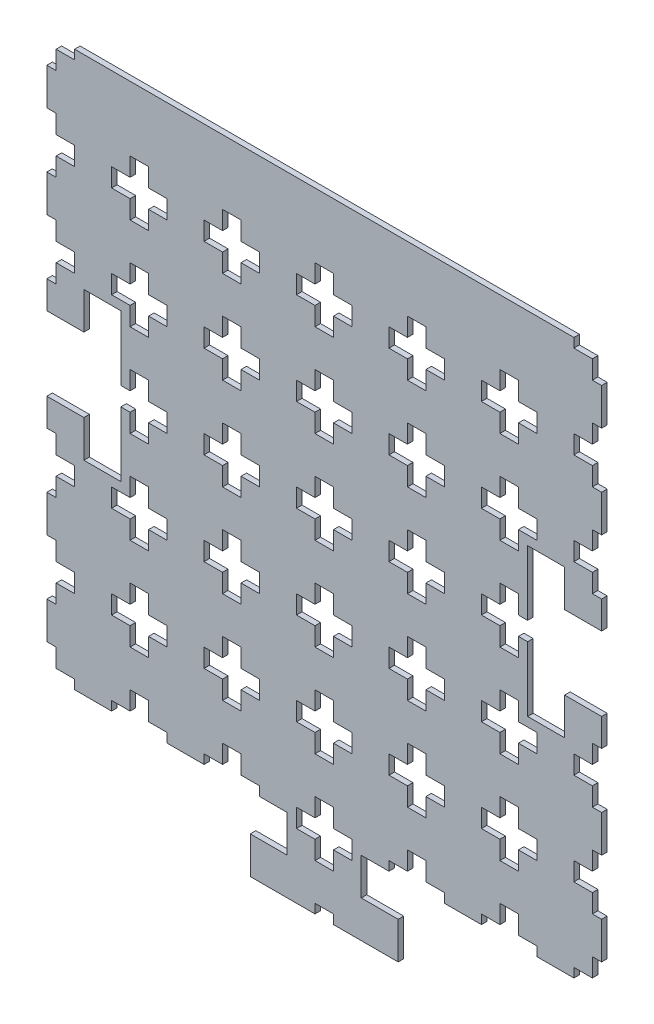
SolidWorks part; units mm, degrees
ref_plane "Plan de face" through (0, 0, 0) normal (0, 0, 1) x (1, 0, 0)
ref_plane "Plan de dessus" through (0, 0, 0) normal (0, 1, 0) x (1, 0, 0)
ref_plane "Plan de droite" through (0, 0, 0) normal (1, 0, 0) x (0, 0, -1)
sketch "Esquisse1" plane through (0, 0, 0) normal (0, 0, 1) x (1, 0, 0)
  line L1 (-218.6403, 173.0618) -> (81.3597, 173.0618)
  line L2 (-218.6403, 173.0618) -> (-218.6403, -126.9382)
  line L3 (-218.6403, -126.9382) -> (81.3597, -126.9382)
  line L4 (81.3597, 173.0618) -> (81.3597, -126.9382)
  dimension "D1" = 300
  dimension "D2" = 300
extrude "Boss.-Extru.1" add sketch "Esquisse1" along normal blind 3
sketch "Esquisse2" plane through (0, 0, 0) normal (0, 0, -1) x (-1, 0, 0)
  line L0 (-81.3597, 138.0618) -> (-76.3597, 138.0618)
  line L2 (-81.3597, -126.9382) -> (-81.3597, 173.0618) construction
  line L3 (-76.3597, 138.0618) -> (-76.3597, 128.0618)
  line L4 (-76.3597, 128.0618) -> (-66.3597, 128.0618)
  line L5 (-66.3597, 128.0618) -> (-66.3597, 118.0618)
  line L6 (-66.3597, 118.0618) -> (-76.3597, 118.0618)
  line L7 (-76.3597, 118.0618) -> (-76.3597, 108.0618)
  line L8 (13.6403, 128.0618) -> (13.6403, 138.0618)
  line L9 (-76.3597, 108.0618) -> (-81.3597, 108.0618)
  line L10 (-81.3597, 88.0618) -> (-76.3597, 88.0618)
  line L11 (-76.3597, 88.0618) -> (-76.3597, 78.0618)
  line L12 (-76.3597, 78.0618) -> (-66.3597, 78.0618)
  line L13 (-66.3597, 78.0618) -> (-66.3597, 68.0618)
  line L14 (-66.3597, 68.0618) -> (-76.3597, 68.0618)
  line L15 (-76.3597, 68.0618) -> (-76.3597, 58.0618)
  line L16 (-76.3597, 58.0618) -> (-81.3597, 58.0618)
  line L17 (-81.3597, 38.0618) -> (-76.3597, 38.0618)
  line L18 (-76.3597, 38.0618) -> (-76.3597, 28.0618)
  line L19 (-76.3597, 28.0618) -> (-66.3597, 28.0618)
  line L20 (-66.3597, 28.0618) -> (-66.3597, 18.0618)
  line L21 (-66.3597, 18.0618) -> (-76.3597, 18.0618)
  line L22 (-76.3597, 18.0618) -> (-76.3597, 8.0618)
  line L23 (-76.3597, 8.0618) -> (-81.3597, 8.0618)
  line L24 (-81.3597, -11.9382) -> (-76.3597, -11.9382)
  line L25 (-76.3597, -11.9382) -> (-76.3597, -21.9382)
  line L26 (-76.3597, -21.9382) -> (-66.3597, -21.9382)
  line L27 (-66.3597, -21.9382) -> (-66.3597, -31.9382)
  line L28 (-66.3597, -31.9382) -> (-76.3597, -31.9382)
  line L29 (-76.3597, -31.9382) -> (-76.3597, -41.9382)
  line L30 (-76.3597, -41.9382) -> (-81.3597, -41.9382)
  line L31 (-81.3597, -61.9382) -> (-76.3597, -61.9382)
  line L32 (-76.3597, -61.9382) -> (-76.3597, -71.9382)
  line L33 (-76.3597, -71.9382) -> (-66.3597, -71.9382)
  line L34 (-66.3597, -71.9382) -> (-66.3597, -81.9382)
  line L35 (-66.3597, -81.9382) -> (-76.3597, -81.9382)
  line L36 (-76.3597, -81.9382) -> (-76.3597, -91.9382)
  line L37 (-76.3597, -91.9382) -> (-81.3597, -91.9382)
  line L38 (-81.3597, -111.9382) -> (-76.3597, -111.9382)
  line L39 (-76.3597, -111.9382) -> (-76.3597, -121.9382)
  line L40 (-76.3597, -121.9382) -> (-66.3597, -121.9382)
  line L41 (-66.3597, -121.9382) -> (-66.3597, -126.9382)
  line L42 (218.6403, -126.9382) -> (-81.3597, -126.9382) construction
  line L43 (-81.3597, 173.0618) -> (218.6403, 173.0618) construction
  line L45 (-66.3597, -131.9382) -> (-76.3597, -131.9382) [skipped]
  line L46 (-76.3597, -131.9382) -> (-76.3597, -141.9382) [skipped]
  line L47 (-76.3597, -141.9382) -> (-81.3597, -141.9382) [skipped]
  line L48 (-66.3597, -121.9382) -> (-66.3597, -131.9382) [skipped]
  line L61 (-36.3597, 128.0618) -> (-36.3597, 138.0618)
  line L62 (-36.3597, 138.0618) -> (-26.3597, 138.0618)
  line L63 (-26.3597, 138.0618) -> (-26.3597, 128.0618)
  line L64 (-26.3597, 128.0618) -> (-16.3597, 128.0618)
  line L65 (-16.3597, 128.0618) -> (-16.3597, 118.0618)
  line L66 (13.6403, 138.0618) -> (23.6403, 138.0618)
  line L67 (3.6403, 128.0618) -> (13.6403, 128.0618)
  line L68 (3.6403, 118.0618) -> (3.6403, 128.0618)
  line L69 (13.6403, 118.0618) -> (3.6403, 118.0618)
  line L70 (13.6403, 108.0618) -> (13.6403, 118.0618)
  line L71 (23.6403, 108.0618) -> (13.6403, 108.0618)
  line L72 (23.6403, 118.0618) -> (23.6403, 108.0618)
  line L73 (33.6403, 118.0618) -> (23.6403, 118.0618)
  line L74 (33.6403, 128.0618) -> (33.6403, 118.0618)
  line L75 (23.6403, 128.0618) -> (33.6403, 128.0618)
  line L76 (23.6403, 138.0618) -> (23.6403, 128.0618)
  line L77 (63.6403, 128.0618) -> (63.6403, 138.0618)
  line L78 (63.6403, 138.0618) -> (73.6403, 138.0618)
  line L79 (53.6403, 128.0618) -> (63.6403, 128.0618)
  line L80 (53.6403, 118.0618) -> (53.6403, 128.0618)
  line L81 (63.6403, 118.0618) -> (53.6403, 118.0618)
  line L82 (63.6403, 108.0618) -> (63.6403, 118.0618)
  line L83 (73.6403, 108.0618) -> (63.6403, 108.0618)
  line L84 (73.6403, 118.0618) -> (73.6403, 108.0618)
  line L85 (83.6403, 118.0618) -> (73.6403, 118.0618)
  line L86 (83.6403, 128.0618) -> (83.6403, 118.0618)
  line L87 (73.6403, 128.0618) -> (83.6403, 128.0618)
  line L88 (73.6403, 138.0618) -> (73.6403, 128.0618)
  line L89 (113.6403, 128.0618) -> (113.6403, 138.0618)
  line L90 (113.6403, 138.0618) -> (123.6403, 138.0618)
  line L91 (103.6403, 128.0618) -> (113.6403, 128.0618)
  line L92 (103.6403, 118.0618) -> (103.6403, 128.0618)
  line L93 (113.6403, 118.0618) -> (103.6403, 118.0618)
  line L94 (113.6403, 108.0618) -> (113.6403, 118.0618)
  line L95 (123.6403, 108.0618) -> (113.6403, 108.0618)
  line L96 (123.6403, 118.0618) -> (123.6403, 108.0618)
  line L97 (133.6403, 118.0618) -> (123.6403, 118.0618)
  line L98 (133.6403, 128.0618) -> (133.6403, 118.0618)
  line L99 (123.6403, 128.0618) -> (133.6403, 128.0618)
  line L100 (123.6403, 138.0618) -> (123.6403, 128.0618)
  line L101 (163.6403, 128.0618) -> (163.6403, 138.0618)
  line L102 (163.6403, 138.0618) -> (173.6403, 138.0618)
  line L103 (153.6403, 128.0618) -> (163.6403, 128.0618)
  line L104 (153.6403, 118.0618) -> (153.6403, 128.0618)
  line L105 (163.6403, 118.0618) -> (153.6403, 118.0618)
  line L106 (163.6403, 108.0618) -> (163.6403, 118.0618)
  line L107 (173.6403, 108.0618) -> (163.6403, 108.0618)
  line L108 (173.6403, 118.0618) -> (173.6403, 108.0618)
  line L109 (183.6403, 118.0618) -> (173.6403, 118.0618)
  line L110 (183.6403, 128.0618) -> (183.6403, 118.0618)
  line L111 (173.6403, 128.0618) -> (183.6403, 128.0618)
  line L112 (173.6403, 138.0618) -> (173.6403, 128.0618)
  line L113 (213.6403, 128.0618) -> (213.6403, 138.0618)
  line L114 (213.6403, 138.0618) -> (223.6403, 138.0618)
  line L115 (203.6403, 128.0618) -> (213.6403, 128.0618)
  line L116 (203.6403, 118.0618) -> (203.6403, 128.0618)
  line L117 (213.6403, 118.0618) -> (203.6403, 118.0618)
  line L118 (213.6403, 108.0618) -> (213.6403, 118.0618)
  line L119 (223.6403, 108.0618) -> (213.6403, 108.0618)
  line L120 (223.6403, 118.0618) -> (223.6403, 108.0618)
  line L121 (233.6403, 118.0618) -> (223.6403, 118.0618)
  line L122 (233.6403, 128.0618) -> (233.6403, 118.0618)
  line L123 (223.6403, 128.0618) -> (233.6403, 128.0618)
  line L124 (223.6403, 138.0618) -> (223.6403, 128.0618)
  line L180 (218.6403, 173.0618) -> (218.6403, -126.9382) construction
  line L186 (13.6403, 78.0618) -> (13.6403, 88.0618)
  line L187 (13.6403, 88.0618) -> (23.6403, 88.0618)
  line L188 (3.6403, 78.0618) -> (13.6403, 78.0618)
  line L189 (3.6403, 68.0618) -> (3.6403, 78.0618)
  line L190 (13.6403, 68.0618) -> (3.6403, 68.0618)
  line L191 (13.6403, 58.0618) -> (13.6403, 68.0618)
  line L192 (23.6403, 58.0618) -> (13.6403, 58.0618)
  line L193 (23.6403, 68.0618) -> (23.6403, 58.0618)
  line L194 (33.6403, 68.0618) -> (23.6403, 68.0618)
  line L195 (33.6403, 78.0618) -> (33.6403, 68.0618)
  line L196 (23.6403, 78.0618) -> (33.6403, 78.0618)
  line L197 (23.6403, 88.0618) -> (23.6403, 78.0618)
  line L198 (63.6403, 78.0618) -> (63.6403, 88.0618)
  line L199 (63.6403, 88.0618) -> (73.6403, 88.0618)
  line L200 (53.6403, 78.0618) -> (63.6403, 78.0618)
  line L201 (53.6403, 68.0618) -> (53.6403, 78.0618)
  line L202 (63.6403, 68.0618) -> (53.6403, 68.0618)
  line L203 (63.6403, 58.0618) -> (63.6403, 68.0618)
  line L204 (73.6403, 58.0618) -> (63.6403, 58.0618)
  line L205 (73.6403, 68.0618) -> (73.6403, 58.0618)
  line L206 (83.6403, 68.0618) -> (73.6403, 68.0618)
  line L207 (83.6403, 78.0618) -> (83.6403, 68.0618)
  line L208 (73.6403, 78.0618) -> (83.6403, 78.0618)
  line L209 (73.6403, 88.0618) -> (73.6403, 78.0618)
  line L210 (113.6403, 78.0618) -> (113.6403, 88.0618)
  line L211 (113.6403, 88.0618) -> (123.6403, 88.0618)
  line L212 (103.6403, 78.0618) -> (113.6403, 78.0618)
  line L213 (103.6403, 68.0618) -> (103.6403, 78.0618)
  line L214 (113.6403, 68.0618) -> (103.6403, 68.0618)
  line L215 (113.6403, 58.0618) -> (113.6403, 68.0618)
  line L216 (123.6403, 58.0618) -> (113.6403, 58.0618)
  line L217 (123.6403, 68.0618) -> (123.6403, 58.0618)
  line L218 (133.6403, 68.0618) -> (123.6403, 68.0618)
  line L219 (133.6403, 78.0618) -> (133.6403, 68.0618)
  line L220 (123.6403, 78.0618) -> (133.6403, 78.0618)
  line L221 (123.6403, 88.0618) -> (123.6403, 78.0618)
  line L222 (163.6403, 78.0618) -> (163.6403, 88.0618)
  line L223 (163.6403, 88.0618) -> (173.6403, 88.0618)
  line L224 (153.6403, 78.0618) -> (163.6403, 78.0618)
  line L225 (153.6403, 68.0618) -> (153.6403, 78.0618)
  line L226 (163.6403, 68.0618) -> (153.6403, 68.0618)
  line L227 (163.6403, 58.0618) -> (163.6403, 68.0618)
  line L228 (173.6403, 58.0618) -> (163.6403, 58.0618)
  line L229 (173.6403, 68.0618) -> (173.6403, 58.0618)
  line L230 (183.6403, 68.0618) -> (173.6403, 68.0618)
  line L231 (183.6403, 78.0618) -> (183.6403, 68.0618)
  line L232 (173.6403, 78.0618) -> (183.6403, 78.0618)
  line L233 (173.6403, 88.0618) -> (173.6403, 78.0618)
  line L234 (213.6403, 78.0618) -> (213.6403, 88.0618)
  line L235 (213.6403, 88.0618) -> (223.6403, 88.0618)
  line L236 (203.6403, 78.0618) -> (213.6403, 78.0618)
  line L237 (203.6403, 68.0618) -> (203.6403, 78.0618)
  line L238 (213.6403, 68.0618) -> (203.6403, 68.0618)
  line L239 (213.6403, 58.0618) -> (213.6403, 68.0618)
  line L240 (223.6403, 58.0618) -> (213.6403, 58.0618)
  line L241 (223.6403, 68.0618) -> (223.6403, 58.0618)
  line L242 (233.6403, 68.0618) -> (223.6403, 68.0618)
  line L243 (233.6403, 78.0618) -> (233.6403, 68.0618)
  line L244 (223.6403, 78.0618) -> (233.6403, 78.0618)
  line L245 (223.6403, 88.0618) -> (223.6403, 78.0618)
  line L246 (13.6403, 28.0618) -> (13.6403, 38.0618)
  line L247 (13.6403, 38.0618) -> (23.6403, 38.0618)
  line L248 (3.6403, 28.0618) -> (13.6403, 28.0618)
  line L249 (3.6403, 18.0618) -> (3.6403, 28.0618)
  line L250 (13.6403, 18.0618) -> (3.6403, 18.0618)
  line L251 (13.6403, 8.0618) -> (13.6403, 18.0618)
  line L252 (23.6403, 8.0618) -> (13.6403, 8.0618)
  line L253 (23.6403, 18.0618) -> (23.6403, 8.0618)
  line L254 (33.6403, 18.0618) -> (23.6403, 18.0618)
  line L255 (33.6403, 28.0618) -> (33.6403, 18.0618)
  line L256 (23.6403, 28.0618) -> (33.6403, 28.0618)
  line L257 (23.6403, 38.0618) -> (23.6403, 28.0618)
  line L258 (63.6403, 28.0618) -> (63.6403, 38.0618)
  line L259 (63.6403, 38.0618) -> (73.6403, 38.0618)
  line L260 (53.6403, 28.0618) -> (63.6403, 28.0618)
  line L261 (53.6403, 18.0618) -> (53.6403, 28.0618)
  line L262 (63.6403, 18.0618) -> (53.6403, 18.0618)
  line L263 (63.6403, 8.0618) -> (63.6403, 18.0618)
  line L264 (73.6403, 8.0618) -> (63.6403, 8.0618)
  line L265 (73.6403, 18.0618) -> (73.6403, 8.0618)
  line L266 (83.6403, 18.0618) -> (73.6403, 18.0618)
  line L267 (83.6403, 28.0618) -> (83.6403, 18.0618)
  line L268 (73.6403, 28.0618) -> (83.6403, 28.0618)
  line L269 (73.6403, 38.0618) -> (73.6403, 28.0618)
  line L270 (113.6403, 28.0618) -> (113.6403, 38.0618)
  line L271 (113.6403, 38.0618) -> (123.6403, 38.0618)
  line L272 (103.6403, 28.0618) -> (113.6403, 28.0618)
  line L273 (103.6403, 18.0618) -> (103.6403, 28.0618)
  line L274 (113.6403, 18.0618) -> (103.6403, 18.0618)
  line L275 (113.6403, 8.0618) -> (113.6403, 18.0618)
  line L276 (123.6403, 8.0618) -> (113.6403, 8.0618)
  line L277 (123.6403, 18.0618) -> (123.6403, 8.0618)
  line L278 (133.6403, 18.0618) -> (123.6403, 18.0618)
  line L279 (133.6403, 28.0618) -> (133.6403, 18.0618)
  line L280 (123.6403, 28.0618) -> (133.6403, 28.0618)
  line L281 (123.6403, 38.0618) -> (123.6403, 28.0618)
  line L282 (163.6403, 28.0618) -> (163.6403, 38.0618)
  line L283 (163.6403, 38.0618) -> (173.6403, 38.0618)
  line L284 (153.6403, 28.0618) -> (163.6403, 28.0618)
  line L285 (153.6403, 18.0618) -> (153.6403, 28.0618)
  line L286 (163.6403, 18.0618) -> (153.6403, 18.0618)
  line L287 (163.6403, 8.0618) -> (163.6403, 18.0618)
  line L288 (173.6403, 8.0618) -> (163.6403, 8.0618)
  line L289 (173.6403, 18.0618) -> (173.6403, 8.0618)
  line L290 (183.6403, 18.0618) -> (173.6403, 18.0618)
  line L291 (183.6403, 28.0618) -> (183.6403, 18.0618)
  line L292 (173.6403, 28.0618) -> (183.6403, 28.0618)
  line L293 (173.6403, 38.0618) -> (173.6403, 28.0618)
  line L294 (213.6403, 28.0618) -> (213.6403, 38.0618)
  line L295 (213.6403, 38.0618) -> (223.6403, 38.0618)
  line L296 (203.6403, 28.0618) -> (213.6403, 28.0618)
  line L297 (203.6403, 18.0618) -> (203.6403, 28.0618)
  line L298 (-66.3597, 173.0618) -> (-66.3597, 168.0618)
  line L299 (-66.3597, 168.0618) -> (-76.3597, 168.0618)
  line L300 (-76.3597, 168.0618) -> (-76.3597, 158.0618)
  line L301 (-76.3597, 158.0618) -> (-81.3597, 158.0618)
  line L302 (218.6403, 158.0618) -> (213.6403, 158.0618)
  line L303 (213.6403, 18.0618) -> (203.6403, 18.0618)
  line L304 (213.6403, 8.0618) -> (213.6403, 18.0618)
  line L305 (223.6403, 8.0618) -> (213.6403, 8.0618)
  line L306 (223.6403, 18.0618) -> (223.6403, 8.0618)
  line L307 (233.6403, 18.0618) -> (223.6403, 18.0618)
  line L308 (233.6403, 28.0618) -> (233.6403, 18.0618)
  line L309 (223.6403, 28.0618) -> (233.6403, 28.0618)
  line L310 (223.6403, 38.0618) -> (223.6403, 28.0618)
  line L311 (13.6403, -21.9382) -> (13.6403, -11.9382)
  line L312 (13.6403, -11.9382) -> (23.6403, -11.9382)
  line L313 (3.6403, -21.9382) -> (13.6403, -21.9382)
  line L314 (3.6403, -31.9382) -> (3.6403, -21.9382)
  line L315 (13.6403, -31.9382) -> (3.6403, -31.9382)
  line L316 (13.6403, -41.9382) -> (13.6403, -31.9382)
  line L317 (23.6403, -41.9382) -> (13.6403, -41.9382)
  line L318 (23.6403, -31.9382) -> (23.6403, -41.9382)
  line L319 (33.6403, -31.9382) -> (23.6403, -31.9382)
  line L320 (33.6403, -21.9382) -> (33.6403, -31.9382)
  line L321 (23.6403, -21.9382) -> (33.6403, -21.9382)
  line L322 (23.6403, -11.9382) -> (23.6403, -21.9382)
  line L323 (63.6403, -21.9382) -> (63.6403, -11.9382)
  line L324 (63.6403, -11.9382) -> (73.6403, -11.9382)
  line L325 (53.6403, -21.9382) -> (63.6403, -21.9382)
  line L326 (53.6403, -31.9382) -> (53.6403, -21.9382)
  line L327 (63.6403, -31.9382) -> (53.6403, -31.9382)
  line L328 (63.6403, -41.9382) -> (63.6403, -31.9382)
  line L329 (73.6403, -41.9382) -> (63.6403, -41.9382)
  line L330 (73.6403, -31.9382) -> (73.6403, -41.9382)
  line L331 (83.6403, -31.9382) -> (73.6403, -31.9382)
  line L332 (83.6403, -21.9382) -> (83.6403, -31.9382)
  line L333 (73.6403, -21.9382) -> (83.6403, -21.9382)
  line L334 (73.6403, -11.9382) -> (73.6403, -21.9382)
  line L335 (113.6403, -21.9382) -> (113.6403, -11.9382)
  line L336 (113.6403, -11.9382) -> (123.6403, -11.9382)
  line L337 (103.6403, -21.9382) -> (113.6403, -21.9382)
  line L338 (103.6403, -31.9382) -> (103.6403, -21.9382)
  line L339 (113.6403, -31.9382) -> (103.6403, -31.9382)
  line L340 (113.6403, -41.9382) -> (113.6403, -31.9382)
  line L341 (123.6403, -41.9382) -> (113.6403, -41.9382)
  line L342 (123.6403, -31.9382) -> (123.6403, -41.9382)
  line L343 (133.6403, -31.9382) -> (123.6403, -31.9382)
  line L344 (133.6403, -21.9382) -> (133.6403, -31.9382)
  line L345 (123.6403, -21.9382) -> (133.6403, -21.9382)
  line L346 (123.6403, -11.9382) -> (123.6403, -21.9382)
  line L347 (163.6403, -21.9382) -> (163.6403, -11.9382)
  line L348 (163.6403, -11.9382) -> (173.6403, -11.9382)
  line L349 (153.6403, -21.9382) -> (163.6403, -21.9382)
  line L350 (153.6403, -31.9382) -> (153.6403, -21.9382)
  line L351 (163.6403, -31.9382) -> (153.6403, -31.9382)
  line L352 (163.6403, -41.9382) -> (163.6403, -31.9382)
  line L353 (173.6403, -41.9382) -> (163.6403, -41.9382)
  line L354 (173.6403, -31.9382) -> (173.6403, -41.9382)
  line L355 (183.6403, -31.9382) -> (173.6403, -31.9382)
  line L356 (213.6403, 158.0618) -> (213.6403, 168.0618)
  line L357 (213.6403, 168.0618) -> (203.6403, 168.0618)
  line L358 (203.6403, 168.0618) -> (203.6403, 173.0618)
  line L363 (183.6403, -21.9382) -> (183.6403, -31.9382)
  line L364 (173.6403, -21.9382) -> (183.6403, -21.9382)
  line L365 (-16.3597, 118.0618) -> (-26.3597, 118.0618)
  line L366 (173.6403, -11.9382) -> (173.6403, -21.9382)
  line L367 (213.6403, -21.9382) -> (213.6403, -11.9382)
  line L368 (213.6403, -11.9382) -> (223.6403, -11.9382)
  line L369 (203.6403, -21.9382) -> (213.6403, -21.9382)
  line L370 (203.6403, -31.9382) -> (203.6403, -21.9382)
  line L371 (-26.3597, 118.0618) -> (-26.3597, 108.0618)
  line L372 (-26.3597, 108.0618) -> (-36.3597, 108.0618)
  line L373 (-36.3597, 108.0618) -> (-36.3597, 118.0618)
  line L374 (-36.3597, 118.0618) -> (-46.3597, 118.0618)
  line L375 (-46.3597, 118.0618) -> (-46.3597, 128.0618)
  line L376 (-46.3597, 128.0618) -> (-36.3597, 128.0618)
  line L377 (213.6403, -31.9382) -> (203.6403, -31.9382)
  line L378 (213.6403, -41.9382) -> (213.6403, -31.9382)
  line L379 (223.6403, -41.9382) -> (213.6403, -41.9382)
  line L380 (223.6403, -31.9382) -> (223.6403, -41.9382)
  line L381 (233.6403, -31.9382) -> (223.6403, -31.9382)
  line L382 (233.6403, -21.9382) -> (233.6403, -31.9382)
  line L383 (223.6403, -21.9382) -> (233.6403, -21.9382)
  line L384 (223.6403, -11.9382) -> (223.6403, -21.9382)
  line L385 (13.6403, -71.9382) -> (13.6403, -61.9382)
  line L386 (13.6403, -61.9382) -> (23.6403, -61.9382)
  line L387 (3.6403, -71.9382) -> (13.6403, -71.9382)
  line L388 (3.6403, -81.9382) -> (3.6403, -71.9382)
  line L389 (13.6403, -81.9382) -> (3.6403, -81.9382)
  line L390 (13.6403, -91.9382) -> (13.6403, -81.9382)
  line L391 (23.6403, -91.9382) -> (13.6403, -91.9382)
  line L392 (23.6403, -81.9382) -> (23.6403, -91.9382)
  line L393 (33.6403, -81.9382) -> (23.6403, -81.9382)
  line L394 (33.6403, -71.9382) -> (33.6403, -81.9382)
  line L395 (23.6403, -71.9382) -> (33.6403, -71.9382)
  line L396 (23.6403, -61.9382) -> (23.6403, -71.9382)
  line L397 (63.6403, -71.9382) -> (63.6403, -61.9382)
  line L398 (63.6403, -61.9382) -> (73.6403, -61.9382)
  line L399 (53.6403, -71.9382) -> (63.6403, -71.9382)
  line L400 (53.6403, -81.9382) -> (53.6403, -71.9382)
  line L401 (63.6403, -81.9382) -> (53.6403, -81.9382)
  line L402 (63.6403, -91.9382) -> (63.6403, -81.9382)
  line L403 (73.6403, -91.9382) -> (63.6403, -91.9382)
  line L404 (73.6403, -81.9382) -> (73.6403, -91.9382)
  line L405 (83.6403, -81.9382) -> (73.6403, -81.9382)
  line L406 (83.6403, -71.9382) -> (83.6403, -81.9382)
  line L407 (73.6403, -71.9382) -> (83.6403, -71.9382)
  line L408 (73.6403, -61.9382) -> (73.6403, -71.9382)
  line L409 (113.6403, -71.9382) -> (113.6403, -61.9382)
  line L410 (113.6403, -61.9382) -> (123.6403, -61.9382)
  line L411 (103.6403, -71.9382) -> (113.6403, -71.9382)
  line L412 (103.6403, -81.9382) -> (103.6403, -71.9382)
  line L413 (113.6403, -81.9382) -> (103.6403, -81.9382)
  line L414 (113.6403, -91.9382) -> (113.6403, -81.9382)
  line L415 (123.6403, -91.9382) -> (113.6403, -91.9382)
  line L416 (123.6403, -81.9382) -> (123.6403, -91.9382)
  line L417 (133.6403, -81.9382) -> (123.6403, -81.9382)
  line L418 (133.6403, -71.9382) -> (133.6403, -81.9382)
  line L419 (123.6403, -71.9382) -> (133.6403, -71.9382)
  line L420 (123.6403, -61.9382) -> (123.6403, -71.9382)
  line L421 (163.6403, -71.9382) -> (163.6403, -61.9382)
  line L422 (163.6403, -61.9382) -> (173.6403, -61.9382)
  line L423 (153.6403, -71.9382) -> (163.6403, -71.9382)
  line L424 (153.6403, -81.9382) -> (153.6403, -71.9382)
  line L425 (163.6403, -81.9382) -> (153.6403, -81.9382)
  line L426 (163.6403, -91.9382) -> (163.6403, -81.9382)
  line L427 (173.6403, -91.9382) -> (163.6403, -91.9382)
  line L428 (173.6403, -81.9382) -> (173.6403, -91.9382)
  line L429 (183.6403, -81.9382) -> (173.6403, -81.9382)
  line L430 (183.6403, -71.9382) -> (183.6403, -81.9382)
  line L431 (173.6403, -71.9382) -> (183.6403, -71.9382)
  line L432 (173.6403, -61.9382) -> (173.6403, -71.9382)
  line L433 (213.6403, -71.9382) -> (213.6403, -61.9382)
  line L434 (213.6403, -61.9382) -> (223.6403, -61.9382)
  line L435 (203.6403, -71.9382) -> (213.6403, -71.9382)
  line L436 (203.6403, -81.9382) -> (203.6403, -71.9382)
  line L437 (213.6403, -81.9382) -> (203.6403, -81.9382)
  line L438 (213.6403, -91.9382) -> (213.6403, -81.9382)
  line L439 (223.6403, -91.9382) -> (213.6403, -91.9382)
  line L440 (223.6403, -81.9382) -> (223.6403, -91.9382)
  line L441 (233.6403, -81.9382) -> (223.6403, -81.9382)
  line L442 (233.6403, -71.9382) -> (233.6403, -81.9382)
  line L443 (223.6403, -71.9382) -> (233.6403, -71.9382)
  line L444 (223.6403, -61.9382) -> (223.6403, -71.9382)
  line L445 (13.6403, -121.9382) -> (13.6403, -111.9382)
  line L446 (13.6403, -111.9382) -> (23.6403, -111.9382)
  line L447 (3.6403, -121.9382) -> (13.6403, -121.9382)
  line L448 (3.6403, -131.9382) -> (3.6403, -121.9382)
  line L449 (13.6403, -131.9382) -> (3.6403, -131.9382)
  line L450 (13.6403, -141.9382) -> (13.6403, -131.9382)
  line L451 (23.6403, -141.9382) -> (13.6403, -141.9382)
  line L452 (23.6403, -131.9382) -> (23.6403, -141.9382)
  line L453 (33.6403, -131.9382) -> (23.6403, -131.9382)
  line L454 (33.6403, -121.9382) -> (33.6403, -131.9382)
  line L455 (23.6403, -121.9382) -> (33.6403, -121.9382)
  line L456 (23.6403, -111.9382) -> (23.6403, -121.9382)
  line L457 (63.6403, -121.9382) -> (63.6403, -111.9382)
  line L458 (63.6403, -111.9382) -> (73.6403, -111.9382)
  line L459 (53.6403, -121.9382) -> (63.6403, -121.9382)
  line L460 (53.6403, -131.9382) -> (53.6403, -121.9382)
  line L461 (63.6403, -131.9382) -> (53.6403, -131.9382)
  line L462 (63.6403, -141.9382) -> (63.6403, -131.9382)
  line L463 (73.6403, -141.9382) -> (63.6403, -141.9382)
  line L464 (73.6403, -131.9382) -> (73.6403, -141.9382)
  line L465 (83.6403, -131.9382) -> (73.6403, -131.9382)
  line L466 (83.6403, -121.9382) -> (83.6403, -131.9382)
  line L467 (73.6403, -121.9382) -> (83.6403, -121.9382)
  line L468 (73.6403, -111.9382) -> (73.6403, -121.9382)
  line L469 (113.6403, -121.9382) -> (113.6403, -111.9382)
  line L470 (113.6403, -111.9382) -> (123.6403, -111.9382)
  line L471 (103.6403, -121.9382) -> (113.6403, -121.9382)
  line L472 (103.6403, -131.9382) -> (103.6403, -121.9382)
  line L473 (113.6403, -131.9382) -> (103.6403, -131.9382)
  line L474 (113.6403, -141.9382) -> (113.6403, -131.9382)
  line L475 (123.6403, -141.9382) -> (113.6403, -141.9382)
  line L476 (123.6403, -131.9382) -> (123.6403, -141.9382)
  line L477 (133.6403, -131.9382) -> (123.6403, -131.9382)
  line L478 (133.6403, -121.9382) -> (133.6403, -131.9382)
  line L479 (123.6403, -121.9382) -> (133.6403, -121.9382)
  line L480 (123.6403, -111.9382) -> (123.6403, -121.9382)
  line L481 (163.6403, -121.9382) -> (163.6403, -111.9382)
  line L482 (163.6403, -111.9382) -> (173.6403, -111.9382)
  line L483 (153.6403, -121.9382) -> (163.6403, -121.9382)
  line L484 (153.6403, -131.9382) -> (153.6403, -121.9382)
  line L485 (163.6403, -131.9382) -> (153.6403, -131.9382)
  line L486 (163.6403, -141.9382) -> (163.6403, -131.9382)
  line L487 (203.6403, 173.0618) -> (218.6403, 173.0618)
  line L488 (218.6403, 173.0618) -> (218.6403, 158.0618)
  line L489 (-81.3597, 158.0618) -> (-81.3597, 173.0618)
  line L490 (-81.3597, 173.0618) -> (-66.3597, 173.0618)
  line L491 (-81.3597, 138.0618) -> (-81.3597, 108.0618)
  line L492 (-81.3597, 88.0618) -> (-81.3597, 58.0618)
  line L494 (-81.3597, 38.0618) -> (-81.3597, 8.0618)
  line L495 (-81.3597, -11.9382) -> (-81.3597, -41.9382)
  line L496 (-81.3597, -61.9382) -> (-81.3597, -91.9382)
  line L497 (-81.3597, -111.9382) -> (-81.3597, -126.9382)
  line L498 (-81.3597, -126.9382) -> (-66.3597, -126.9382)
  line L567 (173.6403, -141.9382) -> (163.6403, -141.9382)
  line L568 (173.6403, -131.9382) -> (173.6403, -141.9382)
  line L569 (183.6403, -131.9382) -> (173.6403, -131.9382)
  line L570 (183.6403, -121.9382) -> (183.6403, -131.9382)
  line L571 (173.6403, -121.9382) -> (183.6403, -121.9382)
  line L572 (173.6403, -111.9382) -> (173.6403, -121.9382)
  line L573 (213.6403, -121.9382) -> (213.6403, -111.9382)
  line L574 (213.6403, -111.9382) -> (223.6403, -111.9382)
  line L575 (203.6403, -121.9382) -> (213.6403, -121.9382)
  line L576 (203.6403, -131.9382) -> (203.6403, -121.9382)
  line L577 (213.6403, -131.9382) -> (203.6403, -131.9382)
  line L578 (213.6403, -141.9382) -> (213.6403, -131.9382)
  line L579 (223.6403, -141.9382) -> (213.6403, -141.9382)
  line L580 (223.6403, -131.9382) -> (223.6403, -141.9382)
  line L581 (233.6403, -131.9382) -> (223.6403, -131.9382)
  line L582 (233.6403, -121.9382) -> (233.6403, -131.9382)
  line L583 (223.6403, -121.9382) -> (233.6403, -121.9382)
  line L584 (223.6403, -111.9382) -> (223.6403, -121.9382)
  line L585 (13.6403, -171.9382) -> (13.6403, -161.9382)
  line L586 (13.6403, -161.9382) -> (23.6403, -161.9382)
  line L587 (3.6403, -171.9382) -> (13.6403, -171.9382)
  line L588 (3.6403, -181.9382) -> (3.6403, -171.9382)
  line L589 (13.6403, -181.9382) -> (3.6403, -181.9382)
  line L590 (13.6403, -191.9382) -> (13.6403, -181.9382)
  line L591 (23.6403, -191.9382) -> (13.6403, -191.9382)
  line L592 (23.6403, -181.9382) -> (23.6403, -191.9382)
  line L593 (33.6403, -181.9382) -> (23.6403, -181.9382)
  line L594 (33.6403, -171.9382) -> (33.6403, -181.9382)
  line L595 (23.6403, -171.9382) -> (33.6403, -171.9382)
  line L596 (23.6403, -161.9382) -> (23.6403, -171.9382)
  line L597 (63.6403, -171.9382) -> (63.6403, -161.9382)
  line L598 (63.6403, -161.9382) -> (73.6403, -161.9382)
  line L599 (53.6403, -171.9382) -> (63.6403, -171.9382)
  line L600 (53.6403, -181.9382) -> (53.6403, -171.9382)
  line L601 (63.6403, -181.9382) -> (53.6403, -181.9382)
  line L602 (63.6403, -191.9382) -> (63.6403, -181.9382)
  line L603 (73.6403, -191.9382) -> (63.6403, -191.9382)
  line L604 (73.6403, -181.9382) -> (73.6403, -191.9382)
  line L605 (83.6403, -181.9382) -> (73.6403, -181.9382)
  line L606 (83.6403, -171.9382) -> (83.6403, -181.9382)
  line L607 (73.6403, -171.9382) -> (83.6403, -171.9382)
  line L608 (73.6403, -161.9382) -> (73.6403, -171.9382)
  line L609 (113.6403, -171.9382) -> (113.6403, -161.9382)
  line L610 (113.6403, -161.9382) -> (123.6403, -161.9382)
  line L611 (103.6403, -171.9382) -> (113.6403, -171.9382)
  line L612 (103.6403, -181.9382) -> (103.6403, -171.9382)
  line L613 (113.6403, -181.9382) -> (103.6403, -181.9382)
  line L614 (113.6403, -191.9382) -> (113.6403, -181.9382)
  line L615 (123.6403, -191.9382) -> (113.6403, -191.9382)
  line L616 (123.6403, -181.9382) -> (123.6403, -191.9382)
  line L617 (133.6403, -181.9382) -> (123.6403, -181.9382)
  line L618 (133.6403, -171.9382) -> (133.6403, -181.9382)
  line L619 (123.6403, -171.9382) -> (133.6403, -171.9382)
  line L620 (123.6403, -161.9382) -> (123.6403, -171.9382)
  line L657 (63.6403, -221.9382) -> (63.6403, -211.9382)
  line L658 (63.6403, -211.9382) -> (73.6403, -211.9382)
  line L659 (53.6403, -221.9382) -> (63.6403, -221.9382)
  line L660 (53.6403, -231.9382) -> (53.6403, -221.9382)
  line L661 (63.6403, -231.9382) -> (53.6403, -231.9382)
  line L662 (63.6403, -241.9382) -> (63.6403, -231.9382)
  line L663 (73.6403, -241.9382) -> (63.6403, -241.9382)
  line L664 (73.6403, -231.9382) -> (73.6403, -241.9382)
  line L665 (83.6403, -231.9382) -> (73.6403, -231.9382)
  line L666 (83.6403, -221.9382) -> (83.6403, -231.9382)
  line L667 (73.6403, -221.9382) -> (83.6403, -221.9382)
  line L668 (73.6403, -211.9382) -> (73.6403, -221.9382)
  line L765 (-36.3597, 78.0618) -> (-36.3597, 88.0618)
  line L766 (-36.3597, 88.0618) -> (-26.3597, 88.0618)
  line L767 (-46.3597, 78.0618) -> (-36.3597, 78.0618)
  line L768 (-46.3597, 68.0618) -> (-46.3597, 78.0618)
  line L769 (-36.3597, 68.0618) -> (-46.3597, 68.0618)
  line L770 (-36.3597, 58.0618) -> (-36.3597, 68.0618)
  line L771 (-26.3597, 58.0618) -> (-36.3597, 58.0618)
  line L772 (-26.3597, 68.0618) -> (-26.3597, 58.0618)
  line L773 (-16.3597, 68.0618) -> (-26.3597, 68.0618)
  line L774 (-16.3597, 78.0618) -> (-16.3597, 68.0618)
  line L775 (-26.3597, 78.0618) -> (-16.3597, 78.0618)
  line L776 (-26.3597, 88.0618) -> (-26.3597, 78.0618)
  line L777 (-36.3597, 28.0618) -> (-36.3597, 38.0618)
  line L778 (-36.3597, 38.0618) -> (-26.3597, 38.0618)
  line L779 (-46.3597, 28.0618) -> (-36.3597, 28.0618)
  line L780 (-46.3597, 18.0618) -> (-46.3597, 28.0618)
  line L781 (-36.3597, 18.0618) -> (-46.3597, 18.0618)
  line L782 (-36.3597, 8.0618) -> (-36.3597, 18.0618)
  line L783 (-26.3597, 8.0618) -> (-36.3597, 8.0618)
  line L784 (-26.3597, 18.0618) -> (-26.3597, 8.0618)
  line L785 (-16.3597, 18.0618) -> (-26.3597, 18.0618)
  line L786 (-16.3597, 28.0618) -> (-16.3597, 18.0618)
  line L787 (-26.3597, 28.0618) -> (-16.3597, 28.0618)
  line L788 (-26.3597, 38.0618) -> (-26.3597, 28.0618)
  line L789 (-36.3597, -21.9382) -> (-36.3597, -11.9382)
  line L790 (-36.3597, -11.9382) -> (-26.3597, -11.9382)
  line L791 (-46.3597, -21.9382) -> (-36.3597, -21.9382)
  line L792 (-46.3597, -31.9382) -> (-46.3597, -21.9382)
  line L793 (-36.3597, -31.9382) -> (-46.3597, -31.9382)
  line L794 (-36.3597, -41.9382) -> (-36.3597, -31.9382)
  line L795 (-26.3597, -41.9382) -> (-36.3597, -41.9382)
  line L796 (-26.3597, -31.9382) -> (-26.3597, -41.9382)
  line L797 (-16.3597, -31.9382) -> (-26.3597, -31.9382)
  line L798 (-16.3597, -21.9382) -> (-16.3597, -31.9382)
  line L799 (-26.3597, -21.9382) -> (-16.3597, -21.9382)
  line L800 (-26.3597, -11.9382) -> (-26.3597, -21.9382)
  line L801 (-36.3597, -71.9382) -> (-36.3597, -61.9382)
  line L802 (-36.3597, -61.9382) -> (-26.3597, -61.9382)
  line L803 (-46.3597, -71.9382) -> (-36.3597, -71.9382)
  line L804 (-46.3597, -81.9382) -> (-46.3597, -71.9382)
  line L805 (-36.3597, -81.9382) -> (-46.3597, -81.9382)
  line L806 (-36.3597, -91.9382) -> (-36.3597, -81.9382)
  line L807 (-26.3597, -91.9382) -> (-36.3597, -91.9382)
  line L808 (-26.3597, -81.9382) -> (-26.3597, -91.9382)
  line L809 (-16.3597, -81.9382) -> (-26.3597, -81.9382)
  line L810 (-16.3597, -71.9382) -> (-16.3597, -81.9382)
  line L811 (-26.3597, -71.9382) -> (-16.3597, -71.9382)
  line L812 (-26.3597, -61.9382) -> (-26.3597, -71.9382)
  line L813 (-36.3597, -121.9382) -> (-36.3597, -111.9382)
  line L814 (-36.3597, -111.9382) -> (-26.3597, -111.9382)
  line L815 (-46.3597, -121.9382) -> (-36.3597, -121.9382)
  line L816 (-46.3597, -131.9382) -> (-46.3597, -121.9382)
  line L817 (-36.3597, -131.9382) -> (-46.3597, -131.9382)
  line L818 (-36.3597, -141.9382) -> (-36.3597, -131.9382)
  line L819 (-26.3597, -141.9382) -> (-36.3597, -141.9382)
  line L820 (-26.3597, -131.9382) -> (-26.3597, -141.9382)
  line L821 (-16.3597, -131.9382) -> (-26.3597, -131.9382)
  line L822 (-16.3597, -121.9382) -> (-16.3597, -131.9382)
  line L823 (-26.3597, -121.9382) -> (-16.3597, -121.9382)
  line L824 (-26.3597, -111.9382) -> (-26.3597, -121.9382)
  line L861 (213.6403, -221.9382) -> (213.6403, -211.9382) [skipped]
  line L862 (213.6403, -211.9382) -> (223.6403, -211.9382) [skipped]
  line L863 (203.6403, -221.9382) -> (213.6403, -221.9382) [skipped]
  line L864 (203.6403, -231.9382) -> (203.6403, -221.9382) [skipped]
  line L865 (213.6403, -231.9382) -> (203.6403, -231.9382) [skipped]
  line L866 (213.6403, -241.9382) -> (213.6403, -231.9382) [skipped]
  line L867 (223.6403, -241.9382) -> (213.6403, -241.9382) [skipped]
  line L868 (223.6403, -231.9382) -> (223.6403, -241.9382) [skipped]
  line L869 (233.6403, -231.9382) -> (223.6403, -231.9382) [skipped]
  line L870 (233.6403, -221.9382) -> (233.6403, -231.9382) [skipped]
  line L871 (223.6403, -221.9382) -> (233.6403, -221.9382) [skipped]
  line L872 (223.6403, -211.9382) -> (223.6403, -221.9382) [skipped]
  line L873 (213.6403, -271.9382) -> (213.6403, -261.9382) [skipped]
  line L874 (213.6403, -261.9382) -> (223.6403, -261.9382) [skipped]
  line L875 (203.6403, -271.9382) -> (213.6403, -271.9382) [skipped]
  line L876 (203.6403, -281.9382) -> (203.6403, -271.9382) [skipped]
  line L877 (213.6403, -281.9382) -> (203.6403, -281.9382) [skipped]
  line L878 (213.6403, -291.9382) -> (213.6403, -281.9382) [skipped]
  line L879 (223.6403, -291.9382) -> (213.6403, -291.9382) [skipped]
  line L880 (223.6403, -281.9382) -> (223.6403, -291.9382) [skipped]
  line L881 (233.6403, -281.9382) -> (223.6403, -281.9382) [skipped]
  line L882 (233.6403, -271.9382) -> (233.6403, -281.9382) [skipped]
  line L883 (223.6403, -271.9382) -> (233.6403, -271.9382) [skipped]
  line L884 (223.6403, -261.9382) -> (223.6403, -271.9382) [skipped]
  line L885 (213.6403, -171.9382) -> (213.6403, -161.9382) [skipped]
  line L886 (213.6403, -161.9382) -> (223.6403, -161.9382) [skipped]
  line L887 (203.6403, -171.9382) -> (213.6403, -171.9382) [skipped]
  line L888 (203.6403, -181.9382) -> (203.6403, -171.9382) [skipped]
  line L889 (213.6403, -181.9382) -> (203.6403, -181.9382) [skipped]
  line L890 (213.6403, -191.9382) -> (213.6403, -181.9382) [skipped]
  line L891 (223.6403, -191.9382) -> (213.6403, -191.9382) [skipped]
  line L892 (223.6403, -181.9382) -> (223.6403, -191.9382) [skipped]
  line L893 (233.6403, -181.9382) -> (223.6403, -181.9382) [skipped]
  line L894 (233.6403, -171.9382) -> (233.6403, -181.9382) [skipped]
  line L895 (223.6403, -171.9382) -> (233.6403, -171.9382) [skipped]
  line L896 (223.6403, -161.9382) -> (223.6403, -171.9382) [skipped]
  line L897 (163.6403, -271.9382) -> (163.6403, -261.9382) [skipped]
  line L898 (163.6403, -261.9382) -> (173.6403, -261.9382) [skipped]
  line L899 (153.6403, -271.9382) -> (163.6403, -271.9382) [skipped]
  line L900 (153.6403, -281.9382) -> (153.6403, -271.9382) [skipped]
  line L901 (163.6403, -281.9382) -> (153.6403, -281.9382) [skipped]
  line L902 (163.6403, -291.9382) -> (163.6403, -281.9382) [skipped]
  line L903 (173.6403, -291.9382) -> (163.6403, -291.9382) [skipped]
  line L904 (173.6403, -281.9382) -> (173.6403, -291.9382) [skipped]
  line L905 (183.6403, -281.9382) -> (173.6403, -281.9382) [skipped]
  line L906 (183.6403, -271.9382) -> (183.6403, -281.9382) [skipped]
  line L907 (173.6403, -271.9382) -> (183.6403, -271.9382) [skipped]
  line L908 (173.6403, -261.9382) -> (173.6403, -271.9382) [skipped]
  line L909 (113.6403, -271.9382) -> (113.6403, -261.9382) [skipped]
  line L910 (113.6403, -261.9382) -> (123.6403, -261.9382) [skipped]
  line L911 (103.6403, -271.9382) -> (113.6403, -271.9382) [skipped]
  line L912 (113.6403, -291.9382) -> (113.6403, -281.9382) [skipped]
  line L913 (123.6403, -291.9382) -> (113.6403, -291.9382) [skipped]
  line L914 (123.6403, -281.9382) -> (123.6403, -291.9382) [skipped]
  line L915 (133.6403, -281.9382) -> (123.6403, -281.9382) [skipped]
  line L916 (133.6403, -271.9382) -> (133.6403, -281.9382) [skipped]
  line L917 (123.6403, -271.9382) -> (133.6403, -271.9382) [skipped]
  line L918 (123.6403, -261.9382) -> (123.6403, -271.9382) [skipped]
  line L919 (103.6403, -281.9382) -> (103.6403, -271.9382) [skipped]
  line L920 (113.6403, -281.9382) -> (103.6403, -281.9382) [skipped]
  line L921 (73.6403, -271.9382) -> (83.6403, -271.9382) [skipped]
  line L922 (73.6403, -261.9382) -> (73.6403, -271.9382) [skipped]
  line L923 (63.6403, -261.9382) -> (73.6403, -261.9382) [skipped]
  line L924 (63.6403, -271.9382) -> (63.6403, -261.9382) [skipped]
  line L925 (53.6403, -271.9382) -> (63.6403, -271.9382) [skipped]
  line L926 (53.6403, -281.9382) -> (53.6403, -271.9382) [skipped]
  line L927 (63.6403, -291.9382) -> (63.6403, -281.9382) [skipped]
  line L928 (63.6403, -281.9382) -> (53.6403, -281.9382) [skipped]
  line L929 (73.6403, -291.9382) -> (63.6403, -291.9382) [skipped]
  line L930 (83.6403, -281.9382) -> (73.6403, -281.9382) [skipped]
  line L931 (83.6403, -271.9382) -> (83.6403, -281.9382) [skipped]
  line L932 (73.6403, -281.9382) -> (73.6403, -291.9382) [skipped]
  line L933 (183.6403, -181.9382) -> (173.6403, -181.9382) [skipped]
  line L934 (163.6403, -171.9382) -> (163.6403, -161.9382) [skipped]
  line L935 (163.6403, -161.9382) -> (173.6403, -161.9382) [skipped]
  line L936 (153.6403, -171.9382) -> (163.6403, -171.9382) [skipped]
  line L937 (163.6403, -191.9382) -> (163.6403, -181.9382) [skipped]
  line L938 (173.6403, -191.9382) -> (163.6403, -191.9382) [skipped]
  line L939 (173.6403, -181.9382) -> (173.6403, -191.9382) [skipped]
  line L940 (183.6403, -171.9382) -> (183.6403, -181.9382) [skipped]
  line L941 (173.6403, -171.9382) -> (183.6403, -171.9382) [skipped]
  line L942 (173.6403, -161.9382) -> (173.6403, -171.9382) [skipped]
  line L943 (153.6403, -181.9382) -> (153.6403, -171.9382) [skipped]
  line L944 (163.6403, -181.9382) -> (153.6403, -181.9382) [skipped]
  line L945 (163.6403, -221.9382) -> (163.6403, -211.9382) [skipped]
  line L946 (163.6403, -211.9382) -> (173.6403, -211.9382) [skipped]
  line L947 (153.6403, -221.9382) -> (163.6403, -221.9382) [skipped]
  line L948 (153.6403, -231.9382) -> (153.6403, -221.9382) [skipped]
  line L949 (163.6403, -231.9382) -> (153.6403, -231.9382) [skipped]
  line L950 (163.6403, -241.9382) -> (163.6403, -231.9382) [skipped]
  line L951 (173.6403, -241.9382) -> (163.6403, -241.9382) [skipped]
  line L952 (173.6403, -231.9382) -> (173.6403, -241.9382) [skipped]
  line L953 (183.6403, -231.9382) -> (173.6403, -231.9382) [skipped]
  line L954 (183.6403, -221.9382) -> (183.6403, -231.9382) [skipped]
  line L955 (173.6403, -221.9382) -> (183.6403, -221.9382) [skipped]
  line L956 (173.6403, -211.9382) -> (173.6403, -221.9382) [skipped]
  line L957 (-26.3597, -241.9382) -> (-36.3597, -241.9382) [skipped]
  line L958 (-36.3597, -271.9382) -> (-36.3597, -261.9382) [skipped]
  line L959 (-36.3597, -261.9382) -> (-26.3597, -261.9382) [skipped]
  line L960 (-46.3597, -271.9382) -> (-36.3597, -271.9382) [skipped]
  line L961 (-46.3597, -281.9382) -> (-46.3597, -271.9382) [skipped]
  line L962 (-36.3597, -281.9382) -> (-46.3597, -281.9382) [skipped]
  line L963 (-36.3597, -291.9382) -> (-36.3597, -281.9382) [skipped]
  line L964 (-26.3597, -291.9382) -> (-36.3597, -291.9382) [skipped]
  line L965 (-26.3597, -281.9382) -> (-26.3597, -291.9382) [skipped]
  line L966 (-16.3597, -281.9382) -> (-26.3597, -281.9382) [skipped]
  line L967 (-16.3597, -271.9382) -> (-16.3597, -281.9382) [skipped]
  line L968 (-26.3597, -271.9382) -> (-16.3597, -271.9382) [skipped]
  line L969 (-26.3597, -261.9382) -> (-26.3597, -271.9382) [skipped]
  line L970 (13.6403, -271.9382) -> (13.6403, -261.9382) [skipped]
  line L971 (13.6403, -261.9382) -> (23.6403, -261.9382) [skipped]
  line L972 (3.6403, -271.9382) -> (13.6403, -271.9382) [skipped]
  line L973 (3.6403, -281.9382) -> (3.6403, -271.9382) [skipped]
  line L974 (13.6403, -281.9382) -> (3.6403, -281.9382) [skipped]
  line L975 (13.6403, -291.9382) -> (13.6403, -281.9382) [skipped]
  line L976 (23.6403, -291.9382) -> (13.6403, -291.9382) [skipped]
  line L977 (23.6403, -281.9382) -> (23.6403, -291.9382) [skipped]
  line L978 (33.6403, -281.9382) -> (23.6403, -281.9382) [skipped]
  line L979 (33.6403, -271.9382) -> (33.6403, -281.9382) [skipped]
  line L980 (23.6403, -271.9382) -> (33.6403, -271.9382) [skipped]
  line L981 (23.6403, -261.9382) -> (23.6403, -271.9382) [skipped]
  line L982 (-36.3597, -221.9382) -> (-36.3597, -211.9382) [skipped]
  line L983 (-36.3597, -211.9382) -> (-26.3597, -211.9382) [skipped]
  line L984 (-46.3597, -221.9382) -> (-36.3597, -221.9382) [skipped]
  line L985 (-46.3597, -231.9382) -> (-46.3597, -221.9382) [skipped]
  line L986 (-36.3597, -231.9382) -> (-46.3597, -231.9382) [skipped]
  line L987 (-36.3597, -241.9382) -> (-36.3597, -231.9382) [skipped]
  line L988 (-26.3597, -231.9382) -> (-26.3597, -241.9382) [skipped]
  line L989 (-16.3597, -231.9382) -> (-26.3597, -231.9382) [skipped]
  line L990 (-16.3597, -221.9382) -> (-16.3597, -231.9382) [skipped]
  line L991 (-26.3597, -221.9382) -> (-16.3597, -221.9382) [skipped]
  line L992 (-26.3597, -211.9382) -> (-26.3597, -221.9382) [skipped]
  line L993 (-36.3597, -171.9382) -> (-36.3597, -161.9382) [skipped]
  line L994 (-36.3597, -161.9382) -> (-26.3597, -161.9382) [skipped]
  line L995 (-46.3597, -171.9382) -> (-36.3597, -171.9382) [skipped]
  line L996 (-46.3597, -181.9382) -> (-46.3597, -171.9382) [skipped]
  line L997 (-36.3597, -181.9382) -> (-46.3597, -181.9382) [skipped]
  line L998 (-36.3597, -191.9382) -> (-36.3597, -181.9382) [skipped]
  line L999 (-26.3597, -191.9382) -> (-36.3597, -191.9382) [skipped]
  line L1000 (-26.3597, -181.9382) -> (-26.3597, -191.9382) [skipped]
  line L1001 (-16.3597, -181.9382) -> (-26.3597, -181.9382) [skipped]
  line L1002 (-16.3597, -171.9382) -> (-16.3597, -181.9382) [skipped]
  line L1003 (-26.3597, -171.9382) -> (-16.3597, -171.9382) [skipped]
  line L1004 (-26.3597, -161.9382) -> (-26.3597, -171.9382) [skipped]
  line L1005 (103.6403, -221.9382) -> (113.6403, -221.9382) [skipped]
  line L1006 (113.6403, -241.9382) -> (113.6403, -231.9382) [skipped]
  line L1007 (113.6403, -221.9382) -> (113.6403, -211.9382) [skipped]
  line L1008 (113.6403, -231.9382) -> (103.6403, -231.9382) [skipped]
  line L1009 (123.6403, -241.9382) -> (113.6403, -241.9382) [skipped]
  line L1010 (123.6403, -231.9382) -> (123.6403, -241.9382) [skipped]
  line L1011 (133.6403, -231.9382) -> (123.6403, -231.9382) [skipped]
  line L1012 (133.6403, -221.9382) -> (133.6403, -231.9382) [skipped]
  line L1013 (123.6403, -221.9382) -> (133.6403, -221.9382) [skipped]
  line L1014 (123.6403, -211.9382) -> (123.6403, -221.9382) [skipped]
  line L1015 (103.6403, -231.9382) -> (103.6403, -221.9382) [skipped]
  line L1016 (113.6403, -211.9382) -> (123.6403, -211.9382) [skipped]
  line L1017 (3.6403, -221.9382) -> (13.6403, -221.9382) [skipped]
  line L1018 (3.6403, -231.9382) -> (3.6403, -221.9382) [skipped]
  line L1019 (13.6403, -231.9382) -> (3.6403, -231.9382) [skipped]
  line L1020 (13.6403, -221.9382) -> (13.6403, -211.9382) [skipped]
  line L1021 (13.6403, -241.9382) -> (13.6403, -231.9382) [skipped]
  line L1022 (23.6403, -241.9382) -> (13.6403, -241.9382) [skipped]
  line L1023 (23.6403, -231.9382) -> (23.6403, -241.9382) [skipped]
  line L1024 (33.6403, -231.9382) -> (23.6403, -231.9382) [skipped]
  line L1025 (33.6403, -221.9382) -> (33.6403, -231.9382) [skipped]
  line L1026 (23.6403, -221.9382) -> (33.6403, -221.9382) [skipped]
  line L1027 (23.6403, -211.9382) -> (23.6403, -221.9382) [skipped]
  line L1028 (13.6403, -211.9382) -> (23.6403, -211.9382) [skipped]
  line L1029 (13.6403, 138.0618) -> (23.6403, 138.0618) [skipped]
  line L1030 (63.6403, 138.0618) -> (73.6403, 138.0618) [skipped]
  line L1031 (113.6403, 138.0618) -> (123.6403, 138.0618) [skipped]
  line L1032 (163.6403, 138.0618) -> (173.6403, 138.0618) [skipped]
  line L1033 (213.6403, 138.0618) -> (223.6403, 138.0618) [skipped]
  line L1034 (3.6403, 128.0618) -> (13.6403, 128.0618) [skipped]
  line L1035 (23.6403, 128.0618) -> (33.6403, 128.0618) [skipped]
  line L1036 (53.6403, 128.0618) -> (63.6403, 128.0618) [skipped]
  line L1037 (73.6403, 128.0618) -> (83.6403, 128.0618) [skipped]
  line L1038 (103.6403, 128.0618) -> (113.6403, 128.0618) [skipped]
  line L1039 (123.6403, 128.0618) -> (133.6403, 128.0618) [skipped]
  line L1040 (153.6403, 128.0618) -> (163.6403, 128.0618) [skipped]
  line L1041 (173.6403, 128.0618) -> (183.6403, 128.0618) [skipped]
  line L1042 (203.6403, 128.0618) -> (213.6403, 128.0618) [skipped]
  line L1043 (223.6403, 128.0618) -> (233.6403, 128.0618) [skipped]
  line L1044 (233.6403, 118.0618) -> (223.6403, 118.0618) [skipped]
  line L1045 (213.6403, 118.0618) -> (203.6403, 118.0618) [skipped]
  line L1046 (183.6403, 118.0618) -> (173.6403, 118.0618) [skipped]
  line L1047 (163.6403, 118.0618) -> (153.6403, 118.0618) [skipped]
  line L1048 (133.6403, 118.0618) -> (123.6403, 118.0618) [skipped]
  line L1049 (113.6403, 118.0618) -> (103.6403, 118.0618) [skipped]
  line L1050 (83.6403, 118.0618) -> (73.6403, 118.0618) [skipped]
  line L1051 (63.6403, 118.0618) -> (53.6403, 118.0618) [skipped]
  line L1052 (33.6403, 118.0618) -> (23.6403, 118.0618) [skipped]
  line L1053 (13.6403, 118.0618) -> (3.6403, 118.0618) [skipped]
  line L1054 (13.6403, 108.0618) -> (13.6403, 118.0618) [skipped]
  line L1055 (13.6403, 128.0618) -> (13.6403, 138.0618) [skipped]
  line L1056 (223.6403, 108.0618) -> (213.6403, 108.0618) [skipped]
  line L1057 (173.6403, 108.0618) -> (163.6403, 108.0618) [skipped]
  line L1058 (123.6403, 108.0618) -> (113.6403, 108.0618) [skipped]
  line L1059 (73.6403, 108.0618) -> (63.6403, 108.0618) [skipped]
  line L1060 (23.6403, 108.0618) -> (13.6403, 108.0618) [skipped]
  line L1061 (3.6403, 118.0618) -> (3.6403, 128.0618) [skipped]
  line L1062 (23.6403, 138.0618) -> (23.6403, 128.0618) [skipped]
  line L1063 (23.6403, 118.0618) -> (23.6403, 108.0618) [skipped]
  line L1064 (33.6403, 128.0618) -> (33.6403, 118.0618) [skipped]
  line L1065 (63.6403, 108.0618) -> (63.6403, 118.0618) [skipped]
  line L1066 (63.6403, 128.0618) -> (63.6403, 138.0618) [skipped]
  line L1067 (53.6403, 118.0618) -> (53.6403, 128.0618) [skipped]
  line L1068 (73.6403, 138.0618) -> (73.6403, 128.0618) [skipped]
  line L1069 (73.6403, 118.0618) -> (73.6403, 108.0618) [skipped]
  line L1070 (83.6403, 128.0618) -> (83.6403, 118.0618) [skipped]
  line L1071 (113.6403, 108.0618) -> (113.6403, 118.0618) [skipped]
  line L1072 (113.6403, 128.0618) -> (113.6403, 138.0618) [skipped]
  line L1073 (103.6403, 118.0618) -> (103.6403, 128.0618) [skipped]
  line L1074 (123.6403, 138.0618) -> (123.6403, 128.0618) [skipped]
  line L1075 (123.6403, 118.0618) -> (123.6403, 108.0618) [skipped]
  line L1076 (133.6403, 128.0618) -> (133.6403, 118.0618) [skipped]
  line L1077 (163.6403, 108.0618) -> (163.6403, 118.0618) [skipped]
  line L1078 (163.6403, 128.0618) -> (163.6403, 138.0618) [skipped]
  line L1079 (153.6403, 118.0618) -> (153.6403, 128.0618) [skipped]
  line L1080 (173.6403, 138.0618) -> (173.6403, 128.0618) [skipped]
  line L1081 (173.6403, 118.0618) -> (173.6403, 108.0618) [skipped]
  line L1082 (183.6403, 128.0618) -> (183.6403, 118.0618) [skipped]
  line L1083 (213.6403, 108.0618) -> (213.6403, 118.0618) [skipped]
  line L1084 (213.6403, 128.0618) -> (213.6403, 138.0618) [skipped]
  line L1085 (203.6403, 118.0618) -> (203.6403, 128.0618) [skipped]
  line L1086 (223.6403, 138.0618) -> (223.6403, 128.0618) [skipped]
  line L1087 (223.6403, 118.0618) -> (223.6403, 108.0618) [skipped]
  line L1088 (233.6403, 128.0618) -> (233.6403, 118.0618) [skipped]
  dimension "D1" = 35
  dimension "D2" = 5
  dimension "D3" = 10
  dimension "D4" = 10
  dimension "D5" = 6
  dimension "D6" = 10
  dimension "D7" = 6
  dimension "D8" = 5
  dimension "D9" = 6
  dimension "D13" = 15
  dimension "D14" = 5
  dimension "D15" = 10
  dimension "D16" = 5
  dimension "D17" = 5
  dimension "D18" = 10
  dimension "D19" = 15
  dimension "D20" = 10
  dimension "D21" = 9
sketch "Esquisse3" plane through (0, 0, 0) normal (0, 0, -1) x (-1, 0, 0)
  line L0 (48.6403, -126.9382) -> (48.6403, -146.9382)
  line L1 (218.6403, -126.9382) -> (-81.3597, -126.9382) construction
  line L2 (48.6403, -146.9382) -> (28.6403, -146.9382)
  line L3 (28.6403, -146.9382) -> (28.6403, -166.9382)
  line L4 (108.6403, -166.9382) -> (28.6403, -166.9382)
  line L9 (108.6403, -166.9382) -> (108.6403, -146.9382)
  line L10 (108.6403, -146.9382) -> (88.6403, -146.9382)
  line L11 (88.6403, -146.9382) -> (88.6403, -126.9382)
  line L12 (48.6403, -126.9382) -> (88.6403, -126.9382)
  dimension "D1" = 130
  dimension "D2" = 130
  dimension "D3" = 20
  dimension "D4" = 20
  dimension "D5" = 20
  dimension "D6" = 20
  dimension "D7" = 20
extrude "Boss.-Extru.5" add sketch "Esquisse3" against normal blind 3
sketch "Esquisse4" plane through (0, 0, 3) normal (0, 0, 1) x (1, 0, 0)
  line L0 (81.3597, 3.0618) -> (81.3597, 43.0618)
  line L1 (81.3597, -126.9382) -> (81.3597, 173.0618) construction
  line L2 (81.3597, 43.0618) -> (61.3597, 43.0618)
  line L3 (61.3597, 43.0618) -> (61.3597, 63.0618)
  line L4 (61.3597, 63.0618) -> (41.3597, 63.0618)
  line L5 (41.3597, 63.0618) -> (41.3597, -16.9382)
  line L6 (41.3597, -16.9382) -> (61.3597, -16.9382)
  line L7 (61.3597, -16.9382) -> (61.3597, 3.0618)
  line L8 (61.3597, 3.0618) -> (81.3597, 3.0618)
  line L9 (81.3597, 38.0618) -> (81.3597, 8.0618) construction
  line L10 (-218.6403, 43.0618) -> (-218.6403, 3.0618)
  line L11 (-218.6403, 173.0618) -> (-218.6403, -126.9382) construction
  line L12 (-218.6403, 43.0618) -> (-198.6403, 43.0618)
  line L13 (-198.6403, 43.0618) -> (-198.6403, 63.0618)
  line L14 (-198.6403, 63.0618) -> (-178.6403, 63.0618)
  line L15 (-178.6403, 63.0618) -> (-178.6403, -16.9382)
  line L16 (-178.6403, -16.9382) -> (-198.6403, -16.9382)
  line L17 (-198.6403, -16.9382) -> (-198.6403, 3.0618)
  line L18 (-198.6403, 3.0618) -> (-218.6403, 3.0618)
  dimension "D2" = 130
  dimension "D3" = 20
  dimension "D4" = 20
  dimension "D5" = 20
  dimension "D6" = 20
  dimension "D7" = 80
  dimension "D9" = 130
  dimension "D10" = 20
  dimension "D11" = 20
  dimension "D12" = 20
  dimension "D13" = 80
  dimension "D14" = 20
extrude "Enlèv. mat.-Extru.4" cut sketch "Esquisse4" against normal through all
extrude "Enlèv. mat.-Extru.5" cut sketch "Esquisse2" against normal through all
